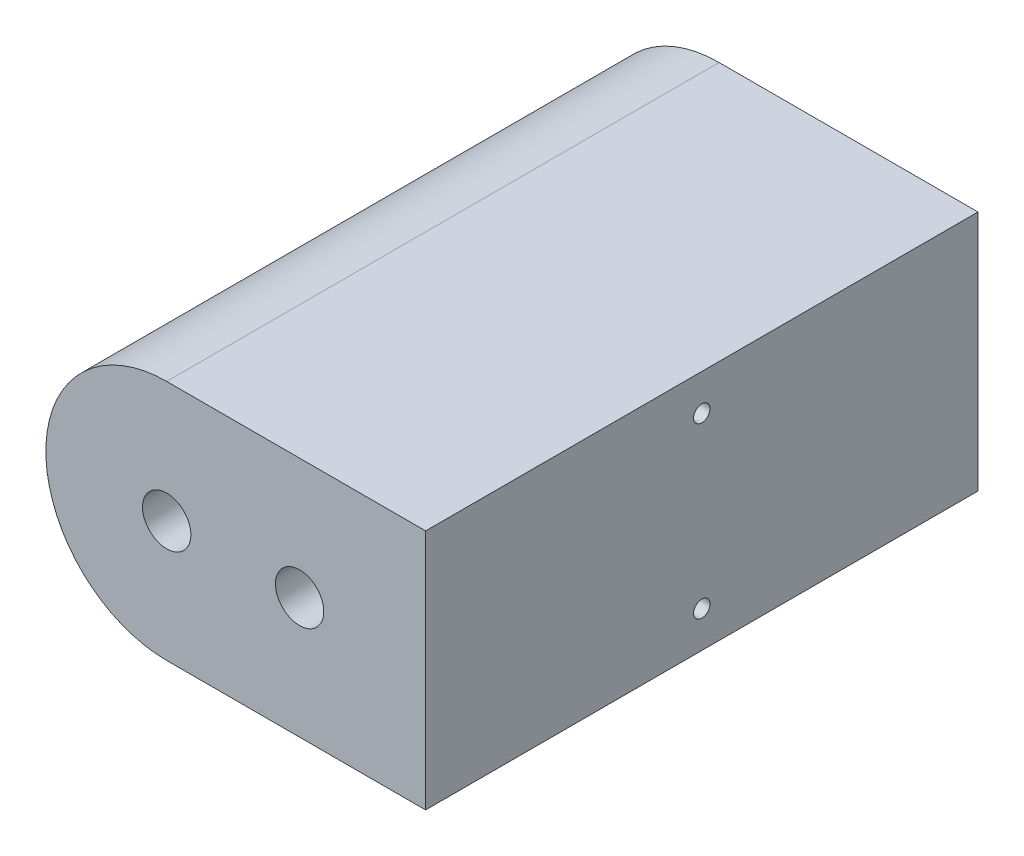
SolidWorks part; units mm, degrees
ref_plane "Front Plane" through (0, 0, 0) normal (0, 0, 1) x (1, 0, 0)
ref_plane "Top Plane" through (0, 0, 0) normal (0, 1, 0) x (1, 0, 0)
ref_plane "Right Plane" through (0, 0, 0) normal (1, 0, 0) x (0, 0, -1)
sketch "Sketch1" plane through (0, 0, 0) normal (0, 0, 1) x (1, 0, 0)
  line L1 (0, 0) -> (-75, 0)
  line L2 (0, 0) -> (0, 70)
  line L3 (0, 70) -> (-75, 70)
  arc A0 (-75, 0) -> (-75, 70) centre (-75, 35) cw
  point P6 (-36.5, 35)
  dimension "D3" = 75
  dimension "D4" = 35
  dimension "D1" = 70
  dimension "D2" = 75
  dimension "D5" = 38.5
extrude "Boss-Extrude1" add sketch "Sketch1" along normal blind 160
scale "Scale1" scale about centroid uniform scaling yes scale factor 1.428571
sketch "Sketch5" plane through (0, 0, -34.2857) normal (0, 0, -1) x (-1, 0, 0)
  line L0 (85.0534, 85) -> (85.0534, -15) construction
  point P4 (85.0534, 35)
  point P5 (30.0534, 35)
  dimension "D1" = 55
hole_wizard "Ø20.0mm Dowel Hole1" positions "3DSketch1" profile "Sketch7" hole size "Ø20.0" standard "ISO" end condition through all
sketch3d "3DSketch1"
  point P0 (-30.0534, 35, -34.2857)
  point P3 (-85.0534, 35, -34.2857)
sketch "Sketch7" plane through (-30.0534, 35, -34.2857) normal (1, 0, 0) x (0, 1, 0)
  line L0 (0, 0) -> (0, 228.5714)
  line L1 (0, 228.5714) -> (10, 228.5714)
  line L2 (10, 228.5714) -> (10, 0)
  line L5 (10, 0) -> (0, 0)
  line L11 (0, -6.35) -> (0, 107.95) construction
  dimension "Thru Hole Dia." = 20
  dimension "Thru Hole Depth" = 228.5714
sketch "Sketch8" plane through (22.0895, 0, 0) normal (1, 0, 0) x (0, 0, -1)
  line L0 (-194.2857, 70) -> (34.2857, 70) construction
  line L1 (-194.2857, -15) -> (-194.2857, 85) construction
  line L2 (34.2857, -15) -> (34.2857, 85) construction
  line L3 (-194.2857, 0) -> (34.2857, 0) construction
  line L4 (-194.2857, 85) -> (34.2857, 85) construction
  line L5 (-194.2857, -15) -> (34.2857, -15) construction
  point P12 (-80, 70)
  point P13 (-80, 0)
  dimension "D1" = 15
  dimension "D2" = 15
hole_wizard "M8 Tapped Hole1" positions "Sketch11" profile "Sketch12" tap size "M8" standard "ISO"
sketch "Sketch11" plane through (22.0895, 0, 0) normal (1, 0, 0) x (0, 0, -1)
  line L0 (-194.2857, 70) -> (34.2857, 70) construction
  point P0 (-80, 70)
  point P4 (-80, 0)
sketch "Sketch12" plane through (22.0895, 70, 80) normal (0, 1, 0) x (0, 0, -1)
  line L0 (0, 0) -> (0, 24.2929)
  line L1 (0, 24.2929) -> (3.4, 22.25)
  line L2 (3.4, 22.25) -> (3.4, 0)
  line L5 (3.4, 0) -> (0, 0)
  line L10 (0, 24.2929) -> (-3.4, 22.25) construction
  line L11 (0, -6.35) -> (0, 107.95) construction
  dimension "Tap Drill Dia." = 6.8
  dimension "Tap Drill Depth" = 22.25
  dimension "Drill Angle" = 118
sketch "Sketch13" plane through (22.0895, 0, 0) normal (1, 0, 0) x (0, 0, -1)
  line L0 (-194.2857, 35) -> (34.2857, 35) construction
  line L1 (-194.2857, -15) -> (-194.2857, 85) construction
  line L2 (34.2857, -15) -> (34.2857, 85) construction
  point P6 (-80, 35)
